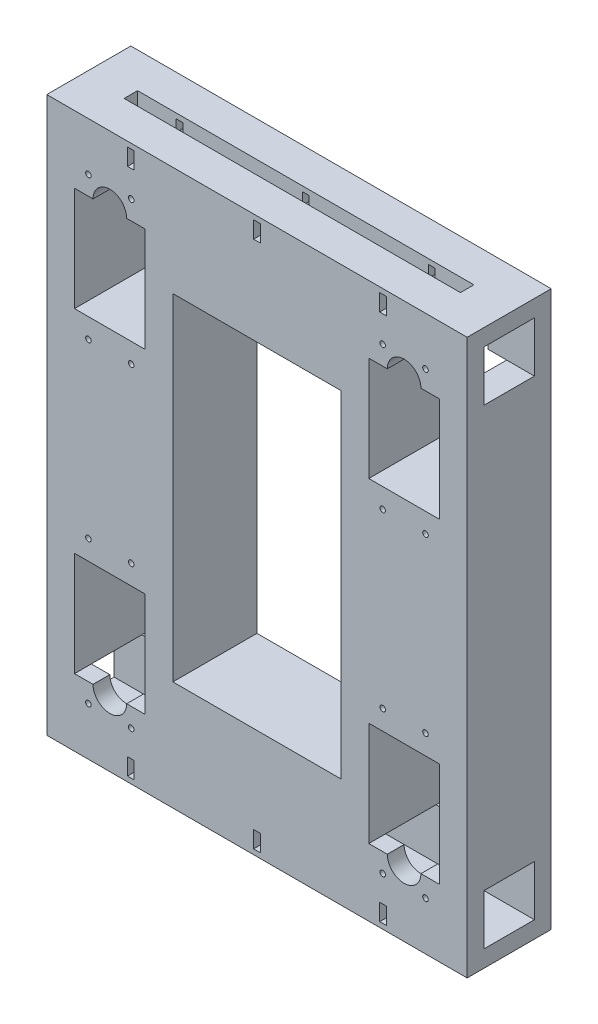
SolidWorks part; units mm, degrees
material "ABS"
ref_plane "Alzado" through (0, 0, 0) normal (0, 0, 1) x (1, 0, 0)
ref_plane "Planta" through (0, 0, 0) normal (0, 1, 0) x (1, 0, 0)
ref_plane "Vista lateral" through (0, 0, 0) normal (1, 0, 0) x (0, 0, -1)
sketch "Croquis1" plane through (0, 0, 0) normal (0, 0, 1) x (1, 0, 0)
  line L1 (0, 0) -> (250, 0)
  line L2 (0, 0) -> (0, 250)
  line L3 (0, 250) -> (250, 250)
  line L4 (250, 0) -> (250, 250)
  line L5 (75, 25) -> (175, 25)
  line L6 (75, 25) -> (75, 225)
  line L7 (75, 225) -> (175, 225)
  line L8 (175, 25) -> (175, 225)
  dimension "D1" = 100
  dimension "D2" = 200
  dimension "D3" = 250
  dimension "D4" = 250
  dimension "D5" = 75
  dimension "D6" = 25
extrude "Saliente-Extruir1" add sketch "Croquis1" along normal blind 50
sketch "Croquis4" plane through (250, 0, 0) normal (1, 0, 0) x (0, 0, -1)
  line L0 (-10, 280) -> (-10, 250)
  line L2 (-25, 280) -> (-40, 280)
  line L3 (-25, 280) -> (-10, 280)
  line L4 (-40, 280) -> (-40, 250)
  line L5 (-50, 250) -> (-40, 250)
  line L6 (-50, 250) -> (-50, 290)
  line L7 (-50, 290) -> (0, 290)
  line L8 (0, 250) -> (0, 290)
  line L9 (-50, 125) -> (90.6612, 125) construction
  line L10 (-50, 0) -> (-50, 250) construction
  line L11 (0, 0) -> (0, -40)
  line L12 (-50, -40) -> (0, -40)
  line L13 (-50, 0) -> (-50, -40)
  line L14 (-50, 0) -> (-40, 0)
  line L15 (-40, -30) -> (-40, 0)
  line L16 (-25, -30) -> (-10, -30)
  line L17 (-25, -30) -> (-40, -30)
  line L18 (-10, -30) -> (-10, 0)
  line L19 (-10, 250) -> (0, 250)
  line L20 (-10, 0) -> (0, 0)
  dimension "D2" = 15
  dimension "D3" = 15
  dimension "D4" = 40
extrude "Saliente-Extruir2" add sketch "Croquis4" against normal through all
sketch "Croquis5" plane through (0, 290, 0) normal (0, 1, 0) x (1, 0, 0)
  line L0 (125, 0) -> (125, -50) construction
  line L1 (0, 0) -> (250, 0) construction
  line L2 (0, -50) -> (250, -50) construction
  line L4 (25, -29) -> (225, -29)
  line L5 (25, -29) -> (25, -21)
  line L6 (25, -21) -> (225, -21)
  line L7 (225, -29) -> (225, -21)
  line L8 (25, -29) -> (225, -21) construction
  line L9 (25, -21) -> (225, -29) construction
  point P6 (125, -25)
  dimension "D1" = 8
  dimension "D2" = 200
extrude "Cortar-Extruir1" cut sketch "Croquis5" against normal blind 10
ref_plane "Plano1" through (0, 125, 0) normal (0, 1, 0) x (1, 0, 0)
sketch "Croquis7" plane through (0, 0, 50) normal (0, 0, 1) x (1, 0, 0)
  line L0 (198, 287) -> (198, 277)
  line L1 (202, 287) -> (202, 277)
  line L2 (127, 287) -> (127, 277)
  line L6 (123, 287) -> (123, 277)
  line L7 (48, 287) -> (48, 277)
  line L8 (52, 287) -> (52, 277)
  line L9 (0, 290) -> (250, 290) construction
  arc A0 (127, 287) -> (123, 287) centre (125, 287) ccw
  arc A1 (123, 277) -> (127, 277) centre (125, 277) ccw
  arc A2 (202, 287) -> (198, 287) centre (200, 287) ccw
  arc A3 (198, 277) -> (202, 277) centre (200, 277) ccw
  arc A4 (52, 287) -> (48, 287) centre (50, 287) ccw
  arc A5 (48, 277) -> (52, 277) centre (50, 277) ccw
  point P0 (125, 289)
  dimension "D1" = 2
  dimension "D2" = 10
  dimension "D5" = 1
  dimension "D3" = 2
  dimension "D4" = 2
extrude "Cortar-Extruir3" cut sketch "Croquis7" against normal through all
sketch "Croquis8" plane through (0, 0, 50) normal (0, 0, 1) x (1, 0, 0)
  line L1 (27.5, 250) -> (16.5, 250)
  line L4 (75, 225) -> (75, 250) construction
  line L5 (75, 250) -> (47.5, 250) construction
  line L6 (16.5, 250) -> (16.5, 188)
  line L7 (16.5, 188) -> (58.5, 188)
  line L8 (58.5, 188) -> (58.5, 250)
  line L9 (58.5, 250) -> (47.5, 250)
  line L10 (37.5, 250) -> (37.5, 229) construction
  line L11 (125, 289) -> (125, -40) construction
  line L12 (0, -40) -> (250, -40) construction
  line L13 (212.5, 250) -> (212.5, 229) construction
  line L14 (175, 250) -> (202.5, 250) construction
  line L15 (175, 225) -> (175, 250) construction
  line L16 (191.5, 250) -> (202.5, 250)
  line L17 (191.5, 188) -> (191.5, 250)
  line L18 (233.5, 188) -> (191.5, 188)
  line L19 (233.5, 250) -> (233.5, 188)
  line L20 (222.5, 250) -> (233.5, 250)
  arc A0 (47.5, 250) -> (27.5, 250) centre (37.5, 250) ccw
  circle A1 centre (37.5, 229) radius 11 construction
  arc A2 (127, 287) -> (123, 287) centre (125, 287) ccw construction
  circle A3 centre (212.5, 229) radius 11 construction
  arc A4 (202.5, 250) -> (222.5, 250) centre (212.5, 250) cw
  dimension "D2" = 20
  dimension "D1" = 37.5
  dimension "D3" = 21
  dimension "D4" = 62
  dimension "D5" = 21
extrude "Cortar-Extruir5" cut sketch "Croquis8" against normal through all
sketch "Croquis9" plane through (0, 0, 50) normal (0, 0, 1) x (1, 0, 0)
  line L0 (37.5, 250) -> (37.5, 229) construction
  line L1 (37.5, 229) -> (50.2279, 241.7279) construction
  line L2 (37.5, 229) -> (50.2279, 216.2721) construction
  line L3 (37.5, 229) -> (24.7721, 216.2721) construction
  line L4 (37.5, 229) -> (24.7721, 241.7279) construction
  line L5 (125, 289) -> (125, -40) construction
  line L6 (0, -40) -> (250, -40) construction
  line L7 (212.5, 229) -> (225.2279, 241.7279) construction
  line L8 (212.5, 229) -> (225.2279, 216.2721) construction
  line L9 (212.5, 229) -> (199.7721, 216.2721) construction
  line L10 (212.5, 229) -> (199.7721, 241.7279) construction
  line L11 (212.5, 250) -> (212.5, 229) construction
  circle A0 centre (37.5, 229) radius 18 construction
  circle A1 centre (24.7721, 241.7279) radius 2 construction
  circle A2 centre (50.2279, 241.7279) radius 2 construction
  circle A3 centre (50.2279, 216.2721) radius 2 construction
  circle A4 centre (24.7721, 216.2721) radius 2 construction
  circle A5 centre (24.7721, 261.2721) radius 2 construction
  circle A6 centre (50.2279, 261.2721) radius 2 construction
  circle A7 centre (24.7721, 176.2721) radius 2 construction
  circle A8 centre (50.2279, 176.2721) radius 2 construction
  arc A9 (127, 287) -> (123, 287) centre (125, 287) ccw construction
  circle A10 centre (225.2279, 216.2721) radius 2 construction
  circle A11 centre (199.7721, 216.2721) radius 2 construction
  circle A12 centre (199.7721, 241.7279) radius 2 construction
  circle A13 centre (225.2279, 241.7279) radius 2 construction
  circle A14 centre (212.5, 229) radius 18 construction
  circle A15 centre (199.7721, 176.2721) radius 2 construction
  circle A16 centre (225.2279, 176.2721) radius 2 construction
  circle A17 centre (199.7721, 261.2721) radius 2 construction
  circle A18 centre (225.2279, 261.2721) radius 2 construction
  point P11 (37.5, 229)
  point P47 (212.5, 229)
  dimension "D2" = 36
  dimension "D5" = 4
  dimension "D1" = 21
  dimension "D3" = 45
  dimension "D6" = 85
  dimension "D7" = 0
  dimension "D8" = 0
  dimension "D9" = 85
  dimension "D4" = 4
hole_wizard "Perforador para roscar para macho de roscar para M41" positions "Croquis10" profile "Croquis11" hole size "M4" standard "ISO"
sketch "Croquis10" plane through (0, 0, 50) normal (0, 0, 1) x (1, 0, 0)
  point P0 (50.2279, 261.2721)
  point P3 (24.7721, 261.2721)
  point P6 (24.7721, 176.2721)
  point P9 (50.2279, 176.2721)
  point P12 (225.2279, 261.2721)
  point P15 (199.7721, 261.2721)
  point P18 (225.2279, 176.2721)
  point P21 (199.7721, 176.2721)
sketch "Croquis11" plane through (50.2279, 261.2721, 50) normal (1, 0, 0) x (0, -1, 0)
  line L0 (0, 0) -> (0, 10.9914)
  line L1 (0, 10.9914) -> (1.65, 10)
  line L2 (1.65, 10) -> (1.65, 0)
  line L5 (1.65, 0) -> (0, 0)
  line L10 (0, 10.9914) -> (-1.65, 10) construction
  line L11 (0, -6.35) -> (0, 107.95) construction
  dimension "Diámetro de taladro" = 3.3
  dimension "Profundidad de taladro" = 10
  dimension "Ángulo de perforador" = 118
hole_wizard "Perforador para roscar para macho de roscar para M42" positions "Croquis12" profile "Croquis13" hole size "M4" standard "ISO"
sketch "Croquis12" plane through (0, 0, 0) normal (0, 0, -1) x (-1, 0, 0)
  point P0 (-50.2279, 261.2721)
  point P3 (-24.7721, 261.2721)
  point P6 (-24.7721, 176.2721)
  point P9 (-50.2279, 176.2721)
  point P12 (-225.2279, 176.2721)
  point P15 (-199.7721, 176.2721)
  point P18 (-199.7721, 261.2721)
  point P21 (-225.2279, 261.2721)
sketch "Croquis13" plane through (50.2279, 261.2721, 0) normal (1, 0, 0) x (0, 1, 0)
  line L0 (0, 0) -> (0, 10.9914)
  line L1 (0, 10.9914) -> (1.65, 10)
  line L2 (1.65, 10) -> (1.65, 0)
  line L5 (1.65, 0) -> (0, 0)
  line L10 (0, 10.9914) -> (-1.65, 10) construction
  line L11 (0, -6.35) -> (0, 107.95) construction
  dimension "Diámetro de taladro" = 3.3
  dimension "Profundidad de taladro" = 10
  dimension "Ángulo de perforador" = 118
mirror "Simetría1" about plane through (0, 125, 0) normal (0, 1, 0) of "Cortar-Extruir1", "Cortar-Extruir3", "Cortar-Extruir5", "Perforador para roscar para macho de roscar para M41", "Perforador para roscar para macho de roscar para M42"
sketch "Croquis14" plane through (0, 0, 0) normal (0, 0, -1) x (-1, 0, 0)
  line L0 (-202, 287) -> (-198, 287)
  line L1 (-202, 277) -> (-198, 277)
  line L2 (-127, 287) -> (-123, 287)
  line L3 (-127, 277) -> (-123, 277)
  line L4 (-52, 287) -> (-48, 287)
  line L5 (-52, 277) -> (-48, 277)
  arc A0 (-198, 287) -> (-202, 287) centre (-200, 287) ccw
  arc A1 (-202, 277) -> (-198, 277) centre (-200, 277) ccw construction
  arc A2 (-202, 277) -> (-198, 277) centre (-200, 277) ccw
  arc A3 (-123, 287) -> (-127, 287) centre (-125, 287) ccw
  arc A4 (-127, 277) -> (-123, 277) centre (-125, 277) ccw
  arc A5 (-48, 287) -> (-52, 287) centre (-50, 287) ccw
  arc A6 (-52, 277) -> (-48, 277) centre (-50, 277) ccw
  dimension "D1" = 3
extrude "Saliente-Extruir4" add sketch "Croquis14" against normal through all
sketch "Croquis15" plane through (0, 290, 0) normal (0, 1, 0) x (1, 0, 0)
  line L1 (25, -21) -> (225, -21)
  line L2 (25, -21) -> (25, -29)
  line L3 (25, -29) -> (225, -29)
  line L4 (225, -21) -> (225, -29)
extrude "Cortar-Extruir6" cut sketch "Croquis15" against normal blind 30
sketch "Croquis16" plane through (250, 0, 0) normal (1, 0, 0) x (0, 0, -1)
  line L1 (-40, 280) -> (-10, 280)
  line L2 (-40, 280) -> (-40, 250)
  line L3 (-40, 250) -> (-10, 250)
  line L4 (-10, 280) -> (-10, 250)
extrude "Cortar-Extruir7" cut sketch "Croquis16" against normal through all
mirror "Simetría4" about plane through (0, 125, 0) normal (0, 1, 0) of "Cortar-Extruir6", "Cortar-Extruir7", "Saliente-Extruir4"
sketch "Croquis17" plane through (0, 277, 0) normal (0, 1, 0) x (1, 0, 0)
  line L0 (52, -40) -> (48, -40) construction
  line L1 (48, -40) -> (48, -50) construction
  line L2 (48, -10) -> (52, -10) construction
  line L3 (52, -10) -> (52, 0) construction
  circle A0 centre (50, -45) radius 1.5
  circle A1 centre (125, -45) radius 1.5
  circle A2 centre (200, -45) radius 1.5
  circle A3 centre (50, -5) radius 1.5
  circle A4 centre (125, -5) radius 1.5
  circle A5 centre (200, -5) radius 1.5
  dimension "D1" = 3
  dimension "D4" = 3
  dimension "D3" = 3
  dimension "D2" = 3
extrude "Cortar-Extruir8" cut sketch "Croquis17" against normal blind 2
ref_plane "Plano2" through (0, 282, 0) normal (0, 1, 0) x (1, 0, 0)
mirror "Simetría5" about plane through (0, 282, 0) normal (0, 1, 0) of "Cortar-Extruir8"
mirror "Simetría6" about plane through (0, 125, 0) normal (0, 1, 0) of "Simetría5", "Cortar-Extruir8"
